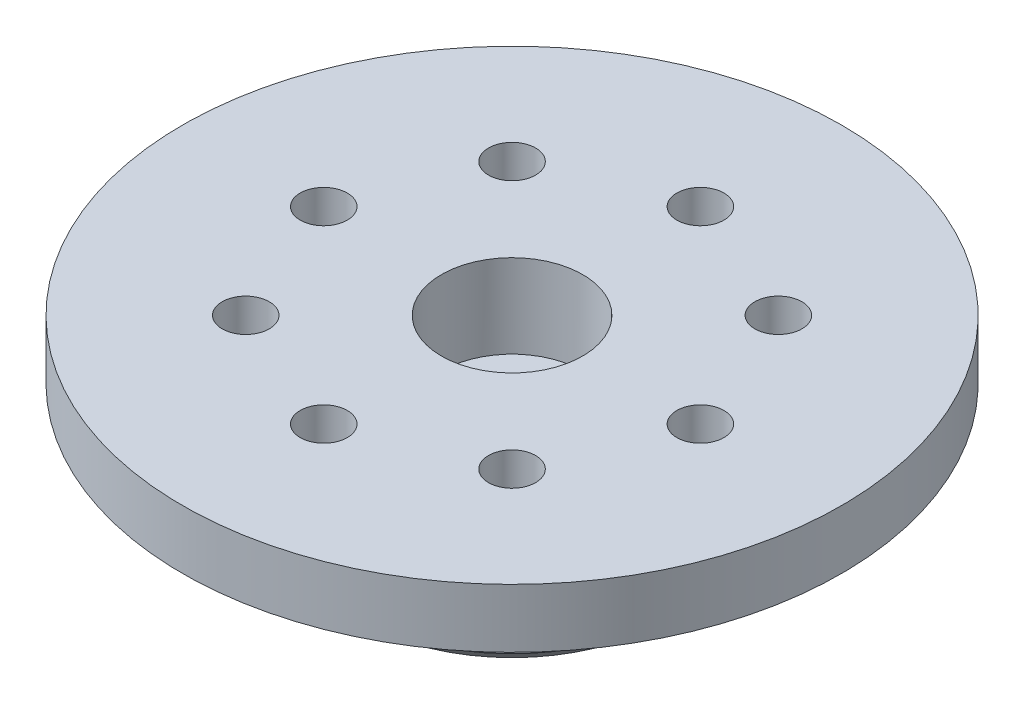
SolidWorks part; units mm, degrees
ref_plane "Ön Düzlem" through (0, 0, 0) normal (0, 0, 1) x (1, 0, 0)
ref_plane "Üst Düzlem" through (0, 0, 0) normal (0, 1, 0) x (1, 0, 0)
ref_plane "Sağ Düzlem" through (0, 0, 0) normal (1, 0, 0) x (0, 0, -1)
sketch "Çizim1" plane through (0, 0, 0) normal (0, 0, 1) x (1, 0, 0)
  line L0 (14, 0) -> (0, 0)
  line L1 (0, 0) -> (0, -2.5)
  line L2 (0, -2.5) -> (14, -2.5)
  line L3 (14, -2.5) -> (14, 0)
  line L4 (0, 0) -> (0, -2.5) construction
revolve "Döndür1" add sketch "Çizim1" angle 360 about L4
sketch "Çizim7" plane through (0, -2.5, 0) normal (0, -1, 0) x (1, 0, 0)
  circle A0 centre (0, 0) radius 5.5
extrude "Kes-Ekstrüzyon1" cut sketch "Çizim7" against normal blind 12.55
sketch "Çizim9" plane through (0, 0, 0) normal (0, 1, 0) x (1, 0, 0)
  circle A0 centre (0, 0) radius 5.5
  circle A1 centre (0, 0) radius 3
  dimension "D1" = 2.5
  dimension "D2" = 11
extrude "Yükseklik-Ekstrüzyon2" add sketch "Çizim9" against normal blind 5.55
sketch "Çizim11" plane through (0, -5.55, 0) normal (0, -1, 0) x (1, 0, 0)
  circle A0 centre (0, 0) radius 3
  circle A1 centre (0, 0) radius 1
  dimension "D1" = 2
extrude "Yükseklik-Ekstrüzyon3" add sketch "Çizim11" against normal blind 2
sketch "Çizim12" plane through (0, 0, 0) normal (0, 1, 0) x (1, 0, 0)
  circle A1 centre (0, 8) radius 1
  circle A2 centre (5.6569, 5.6569) radius 1
  circle A3 centre (8, 0) radius 1
  circle A4 centre (5.6569, -5.6569) radius 1
  circle A5 centre (0, -8) radius 1
  circle A6 centre (-5.6569, -5.6569) radius 1
  circle A7 centre (-8, 0) radius 1
  circle A8 centre (-5.6569, 5.6569) radius 1
  point P22 (0, 0)
  dimension "D1" = 2
  dimension "D2" = 2
  dimension "D3" = 8
extrude "Kes-Ekstrüzyon2" cut sketch "Çizim12" against normal blind 10
sketch "Çizim16" plane through (0, -2.5, 0) normal (0, -1, 0) x (1, 0, 0)
  circle A0 centre (0, 0) radius 5.5
  circle A1 centre (0, 0) radius 7
  dimension "D1" = 11
  dimension "D2" = 1.5
extrude "Yükseklik-Ekstrüzyon4" add sketch "Çizim16" along normal blind 5.5
chamfer "Pah1" distance 0.5 angle 45 1 edges at (0, -8, -7)
sketch "Çizim17" plane through (0, -2.5, 0) normal (0, -1, 0) x (1, 0, 0)
  circle A0 centre (0, 0) radius 7
  circle A1 centre (0, 0) radius 5.8
  dimension "D1" = 14
  dimension "D2" = 1.2
extrude "Kes-Ekstrüzyon3" cut sketch "Çizim17" along normal blind 2
chamfer "Pah2" distance 1 angle 45 1 edges at (0, -4.5, -5.8)
